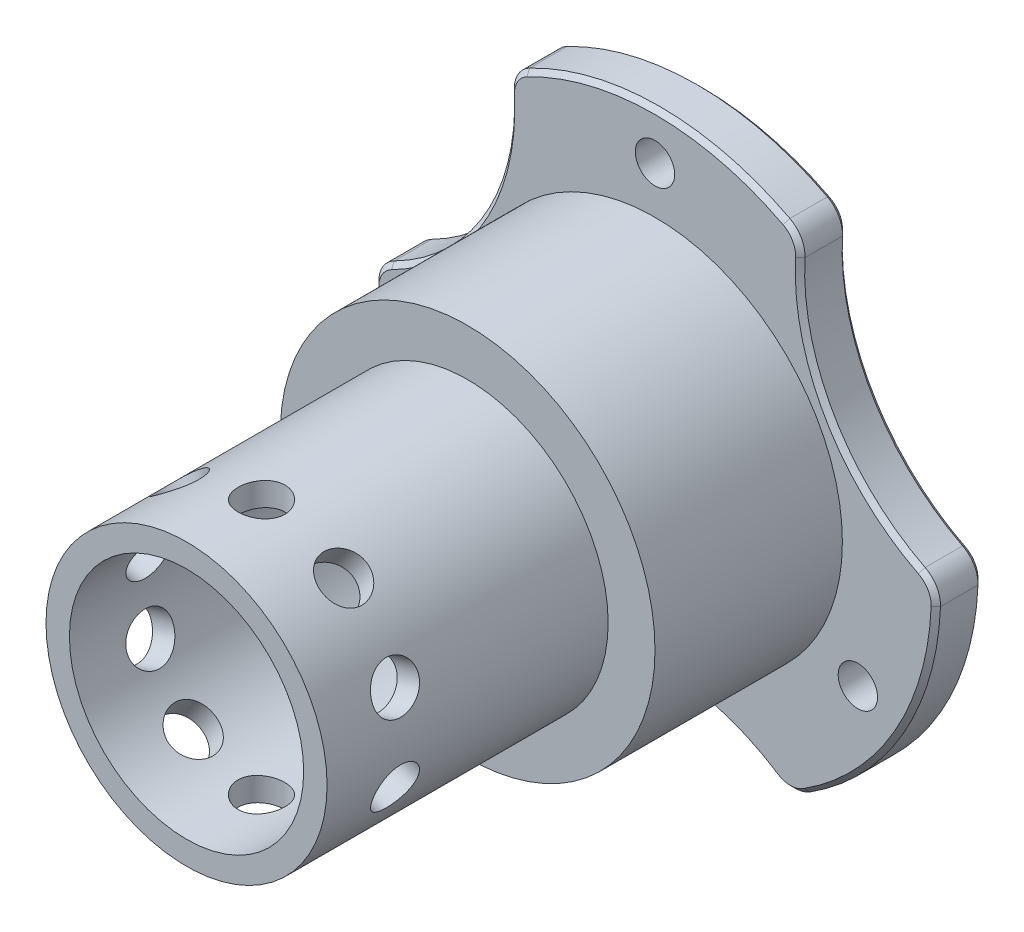
SolidWorks part; units mm, degrees
material "2024 合金"
ref_plane "正面" through (0, 0, 0) normal (0, 0, 1) x (1, 0, 0)
ref_plane "平面" through (0, 0, 0) normal (0, 1, 0) x (1, 0, 0)
ref_plane "右側面" through (0, 0, 0) normal (1, 0, 0) x (0, 0, -1)
sketch "ｽｹｯﾁ1" plane through (0, 0, 0) normal (0, 0, 1) x (1, 0, 0)
  line L0 (-25.9808, 15) -> (25.9808, 15) construction
  line L1 (25.9808, 15) -> (0, -30) construction
  line L2 (0, -30) -> (-25.9808, 15) construction
  line L3 (-38.9711, 22.5) -> (0, -45) construction
  line L4 (0, -45) -> (38.9711, 22.5) construction
  line L5 (38.9711, 22.5) -> (-38.9711, 22.5) construction
  circle A0 centre (0, 0) radius 30
  circle A1 centre (0, 0) radius 45 construction
  arc A2 (-29.9898, 0.784) -> (-15.6738, 25.5799) centre (-38.9711, 22.5) ccw
  arc A3 (15.6738, 25.5799) -> (29.9898, 0.784) centre (38.9711, 22.5) ccw
  circle A4 centre (0, 0) radius 25 construction
  arc A5 (14.3159, -26.3639) -> (-14.3159, -26.3639) centre (0, -45) ccw
  dimension "D1" = 60
  dimension "D2" = 90
  dimension "D3" = 5
  dimension "D4" = 47
extrude "ﾎﾞｽ - 押し出し1" add sketch "ｽｹｯﾁ1" along normal blind 5 contours A5 A0 A3 A2
sketch "ｽｹｯﾁ2" plane through (0, 0, 0) normal (0, 0, -1) x (-1, 0, 0)
  line L0 (0, 25) -> (-21.6506, -12.5) construction
  line L1 (-21.6506, -12.5) -> (21.6506, -12.5) construction
  line L2 (21.6506, -12.5) -> (0, 25) construction
  circle A0 centre (0, 0) radius 25 construction
  circle A1 centre (0, 25) radius 2.1
  circle A2 centre (-21.6506, -12.5) radius 2.1
  circle A3 centre (21.6506, -12.5) radius 2.1
  dimension "D1" = 4.2
extrude "ｶｯﾄ - 押し出し1" cut sketch "ｽｹｯﾁ2" against normal blind 5
cosmetic thread "ねじ山1" parameters "D2"=5
cosmetic thread "ねじ山2" parameters "D2"=5
cosmetic thread "ねじ山3" parameters "D2"=5
sketch "ｽｹｯﾁ3" plane through (0, 0, 5) normal (0, 0, 1) x (1, 0, 0)
  circle A0 centre (0, 0) radius 20
  dimension "D1" = 40
extrude "ﾎﾞｽ - 押し出し2" add sketch "ｽｹｯﾁ3" along normal blind 50
sketch "ｽｹｯﾁ4" plane through (0, 0, 0) normal (0, 0, -1) x (-1, 0, 0)
  circle A0 centre (0, 0) radius 15.5
  dimension "D1" = 31
extrude "ｶｯﾄ - 押し出し2" cut sketch "ｽｹｯﾁ4" against normal blind 12
sketch "ｽｹｯﾁ9" plane through (0, 0, 55) normal (0, 0, 1) x (1, 0, 0)
  circle A0 centre (0, 0) radius 15
  circle A1 centre (0, 0) radius 20
  circle A2 centre (0, 0) radius 20 construction
  dimension "D1" = 30
extrude "ｶｯﾄ - 押し出し7" cut sketch "ｽｹｯﾁ9" against normal blind 30
fillet "ﾌｨﾚｯﾄ1" radius 3 6 edges at (14.3159, -26.3639, 2.5) (-14.3159, -26.3639, 2.5) (-29.9898, 0.784, 2.5) (-15.6738, 25.5799, 2.5) (15.6738, 25.5799, 2.5) (29.9898, 0.784, 2.5)
chamfer "面取り1" distance 0.5 angle 45 24 edges at (-18.6195, 10.75, 5) (-25.9808, -15, 5) (25.9808, -15, 5) (0, 30, 5) (0, -21.5, 5) (18.6195, 10.75, 5) (-25.9808, -15, 0) (0, 30, 0) (25.9808, -15, 0) (-18.6195, 10.75, 0) (0, -21.5, 0) (18.6195, 10.75, 0) (-29.5654, 0.3856, 5) (-14.4487, -25.7972, 5) (-15.1166, 25.4115, 5) (14.4487, -25.7972, 5) (15.1166, 25.4115, 5) (29.5654, 0.3856, 5) (-29.5654, 0.3856, 0) (-14.4487, -25.7972, 0) (-15.1166, 25.4115, 0) (14.4487, -25.7972, 0) (15.1166, 25.4115, 0) (29.5654, 0.3856, 0)
chamfer "面取り2" distance 3 angle 45 1 edges at (-15.5, 0, 0)
ref_plane "平面2" through (0, 0, 47) normal (0, 0, 1) x (1, 0, 0)
sketch "ｽｹｯﾁ11" plane through (0, 0, 47) normal (0, 0, 1) x (1, 0, 0)
  line L0 (0, 15) -> (0, -15) construction
  circle A0 centre (0, 0) radius 15 construction
  point P17 (0, 0)
ref_plane "平面3" through (0, 0, 47) normal (0, -1, 0) x (-1, 0, 0)
sketch "ｽｹｯﾁ12" plane through (0, 0, 47) normal (0, -1, 0) x (-1, 0, 0)
  circle A0 centre (0, 0) radius 2.5
  dimension "D1" = 5
extrude "ｶｯﾄ - 押し出し8" cut sketch "ｽｹｯﾁ12" along normal through all both and the other way through all
sketch "ｽｹｯﾁ14" plane through (0, 0, 55) normal (0, 0, 1) x (1, 0, 0)
  circle A0 centre (0, 0) radius 12.5
  dimension "D1" = 25
extrude "ｶｯﾄ - 押し出し9" cut sketch "ｽｹｯﾁ14" against normal blind 42
sketch "ｽｹｯﾁ15" plane through (0, 0, 13) normal (0, 0, 1) x (1, 0, 0)
  circle A0 centre (0, 0) radius 7.5
  dimension "D1" = 15
extrude "ｶｯﾄ - 押し出し10" cut sketch "ｽｹｯﾁ15" against normal through all
ref_axis "軸2" through (0, 0, 13) along (0, 0, 1)
pattern_circular "円形ﾊﾟﾀｰﾝ2" count 5 over 360 about axis through (0, 0, 13) along (0, 0, 1) of "ｶｯﾄ - 押し出し8"
sketch "ｽｹｯﾁ16" plane through (0, 0, 0) normal (0, 0, -1) x (-1, 0, 0)
  line L0 (0, 25) -> (0, 0) construction
